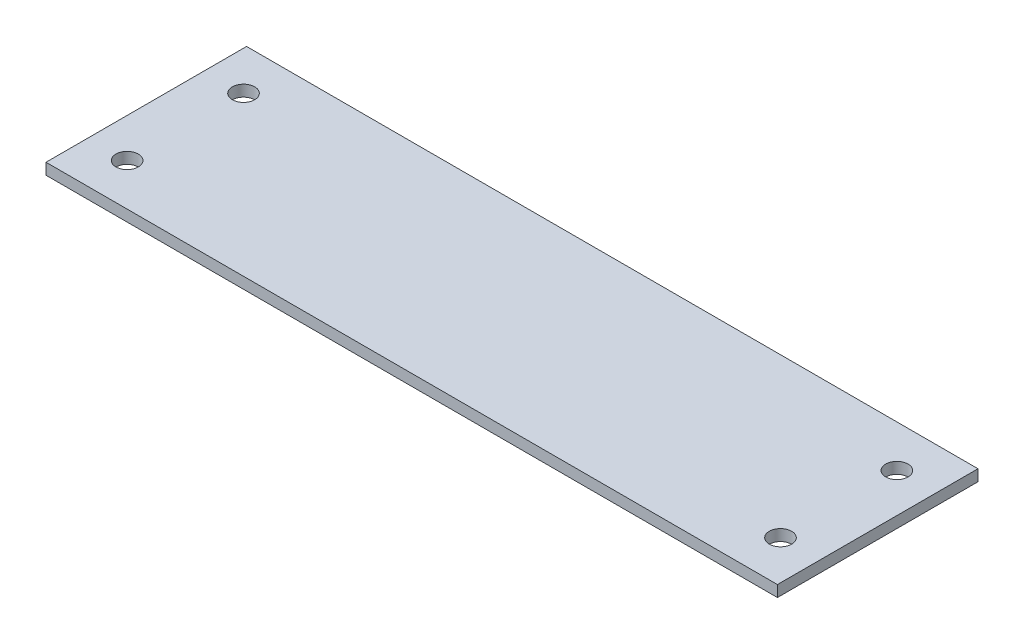
SolidWorks part; units mm, degrees
ref_plane "Front Plane" through (0, 0, 0) normal (0, 0, 1) x (1, 0, 0)
ref_plane "Top Plane" through (0, 0, 0) normal (0, 1, 0) x (1, 0, 0)
ref_plane "Right Plane" through (0, 0, 0) normal (1, 0, 0) x (0, 0, -1)
sketch "Sketch1" plane through (0, 0, 0) normal (0, 1, 0) x (1, 0, 0)
  line L0 (-51.875, 0) -> (51.875, 0) construction
  line L1 (51.875, -14.225) -> (-51.875, -14.225)
  line L2 (51.875, -14.225) -> (51.875, 14.225)
  line L3 (51.875, 14.225) -> (-51.875, 14.225)
  line L4 (-51.875, -14.225) -> (-51.875, 14.225)
  line L5 (0, 14.225) -> (0, -14.225) construction
  point P0 (0, 0)
  point P12 (0, 0)
  dimension "D1" = 28.45
  dimension "D2" = 103.75
extrude "Boss-Extrude1" add sketch "Sketch1" along normal blind 1.6
sketch "Sketch2" plane through (0, 1.6, 0) normal (0, 1, 0) x (1, 0, 0)
  line L0 (51.875, 14.225) -> (-51.875, 14.225) construction
  line L1 (51.875, -14.225) -> (51.875, 14.225) construction
  line L2 (-51.875, 0) -> (51.875, 0) construction
  line L3 (0, 14.225) -> (0, -14.225) construction
  line L4 (-51.875, 0) -> (51.875, 0) construction
  line L5 (0, 14.225) -> (0, -14.225) construction
  circle A0 centre (46.3378, 8.256) radius 1.5875
  circle A1 centre (46.3378, -8.256) radius 1.5875
  circle A2 centre (-46.3378, 8.256) radius 1.5875
  circle A3 centre (-46.3378, -8.256) radius 1.5875
  dimension "D1" = 3.175
  dimension "D2" = 5.969
  dimension "D3" = 5.5372
extrude "Cut-Extrude1" cut sketch "Sketch2" against normal through all
